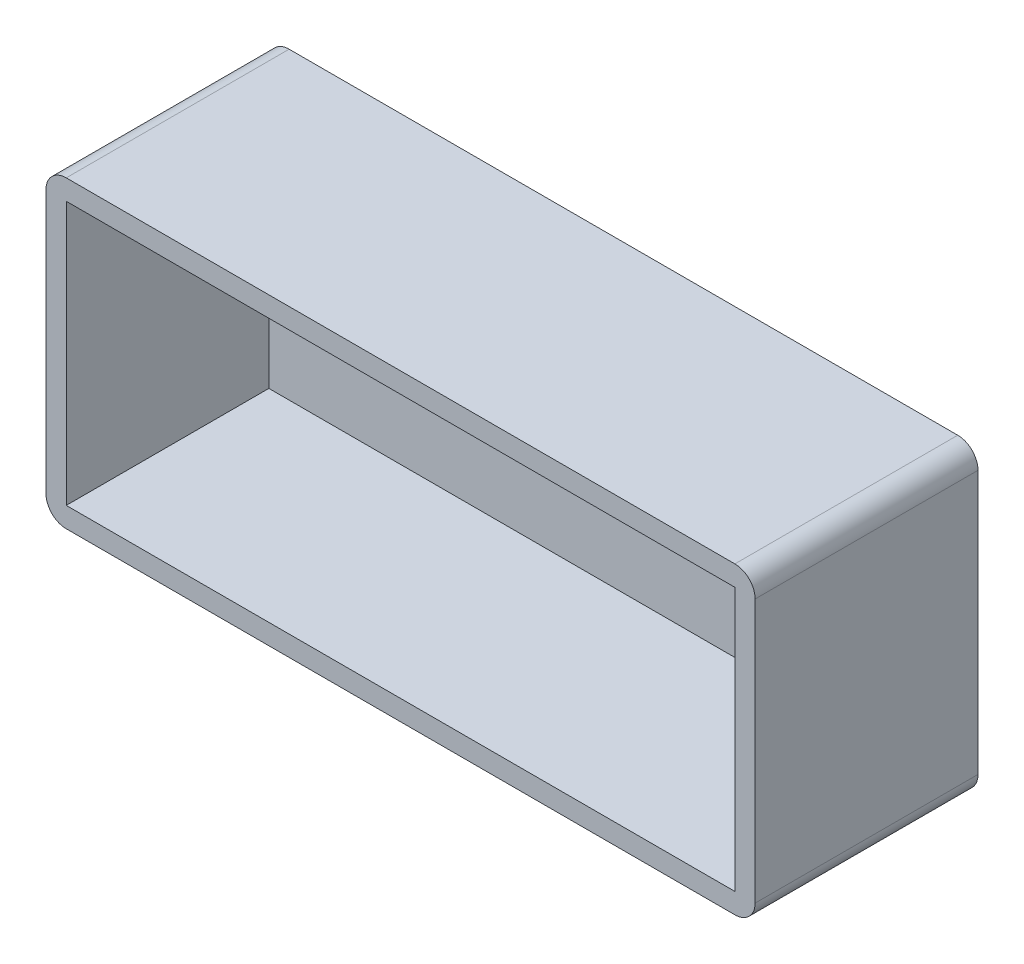
SolidWorks part; units mm, degrees
ref_plane "Alzado" through (0, 0, 0) normal (0, 0, 1) x (1, 0, 0)
ref_plane "Planta" through (0, 0, 0) normal (0, 1, 0) x (1, 0, 0)
ref_plane "Vista lateral" through (0, 0, 0) normal (1, 0, 0) x (0, 0, -1)
sketch "Croquis1" plane through (0, 0, 0) normal (0, 0, 1) x (1, 0, 0)
  line L1 (0, 0) -> (70, 0)
  line L2 (0, 0) -> (0, 30)
  line L3 (0, 30) -> (70, 30)
  line L4 (70, 0) -> (70, 30)
extrude "Saliente-Extruir4" add sketch "Croquis1" along normal blind 22
sketch "Croquis5" plane through (0, 0, 22) normal (0, 0, 1) x (1, 0, 0)
  line L4 (2, 28) -> (68, 28)
  line L5 (2, 28) -> (2, 2)
  line L6 (2, 2) -> (68, 2)
  line L7 (68, 28) -> (68, 2)
extrude "Cortar-Extruir1" cut sketch "Croquis5" against normal blind 20
sketch "Croquis6" plane through (0, 0, 2) normal (0, 0, 1) x (1, 0, 0)
  line L0 (10, 15) -> (24, 15) construction
  line L3 (10, 17) -> (24, 17)
  line L4 (10, 13) -> (24, 13)
  line L8 (60, 15) -> (46, 15) construction
  line L9 (60, 17) -> (46, 17)
  line L10 (60, 13) -> (46, 13)
  arc A0 (10, 17) -> (10, 13) centre (10, 15) ccw
  arc A1 (24, 13) -> (24, 17) centre (24, 15) ccw
  arc A2 (60, 17) -> (60, 13) centre (60, 15) cw
  arc A3 (46, 13) -> (46, 17) centre (46, 15) cw
  point P1 (17, 15)
  point P15 (53, 15)
extrude "Cortar-Extruir3" cut sketch "Croquis6" against normal blind 20 contours L4 A1 L3 A0 | L9 A3 L10 A2
fillet "Redondeo2" radius 2 1 edges at (70, 0, 11)
fillet "Redondeo3" radius 2 1 edges at (70, 30, 11)
fillet "Redondeo4" radius 2 1 edges at (0, 0, 11)
fillet "Redondeo5" radius 2 1 edges at (0, 30, 11)
